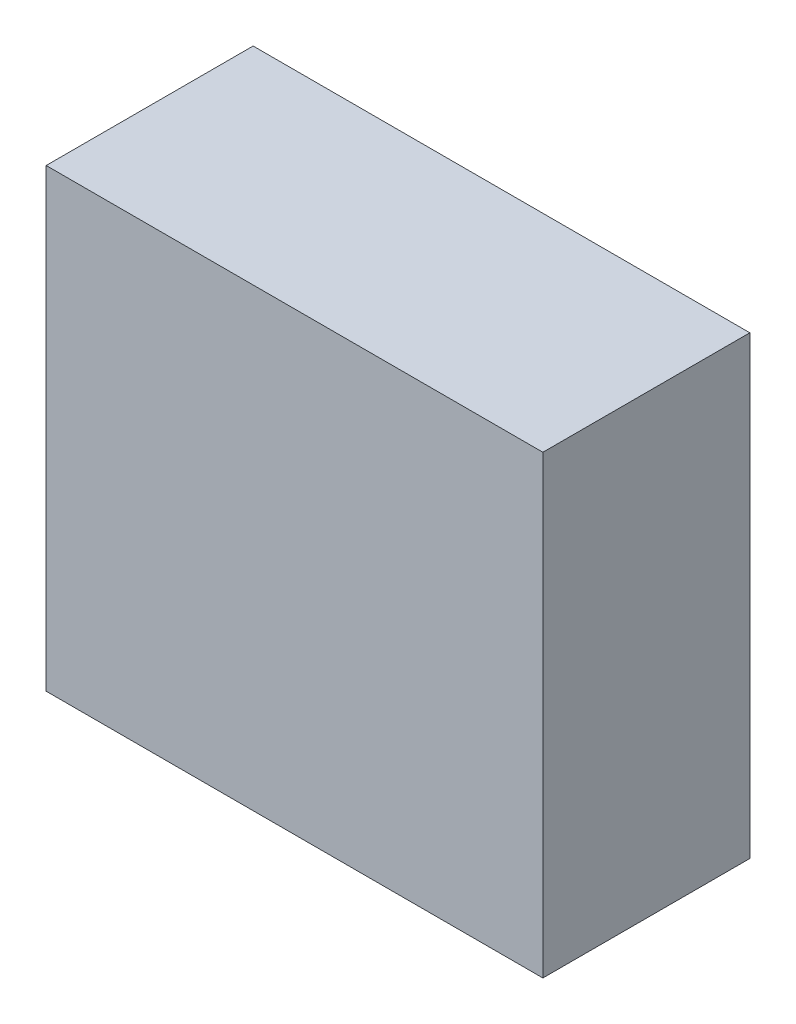
SolidWorks part; units mm, degrees
ref_plane "Front Plane" through (0, 0, 0) normal (0, 0, 1) x (1, 0, 0)
ref_plane "Top Plane" through (0, 0, 0) normal (0, 1, 0) x (1, 0, 0)
ref_plane "Right Plane" through (0, 0, 0) normal (1, 0, 0) x (0, 0, -1)
sketch "Sketch1" plane through (0, 0, 0) normal (0, 0, 1) x (1, 0, 0)
  line L1 (76.2, 69.85) -> (-76.2, 69.85)
  line L2 (76.2, 69.85) -> (76.2, -69.85)
  line L3 (76.2, -69.85) -> (-76.2, -69.85)
  line L4 (-76.2, 69.85) -> (-76.2, -69.85)
  line L5 (76.2, 69.85) -> (-76.2, -69.85) construction
  line L6 (76.2, -69.85) -> (-76.2, 69.85) construction
  point P0 (0, 0)
  dimension "D1" = 139.7
  dimension "D2" = 152.4
extrude "Boss-Extrude1" add sketch "Sketch1" along normal blind 63.5
